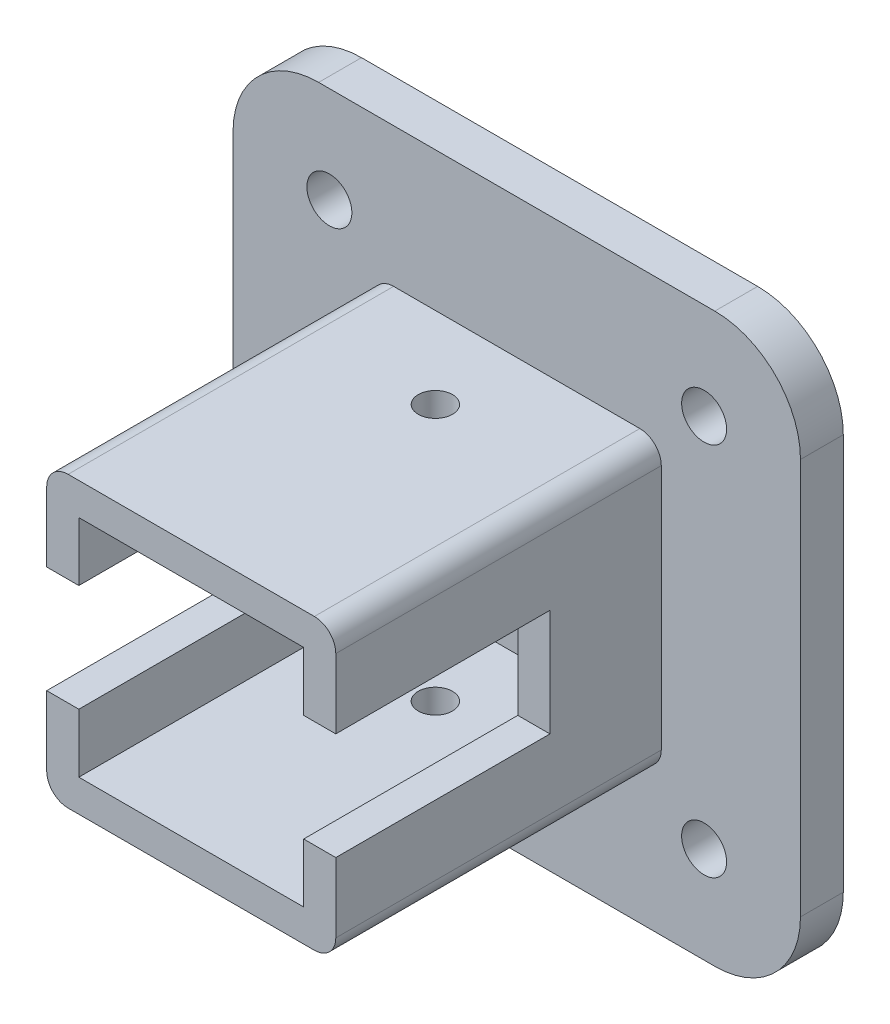
SolidWorks part; units mm, degrees
ref_plane "Front Plane" through (0, 0, 0) normal (0, 0, 1) x (1, 0, 0)
ref_plane "Top Plane" through (0, 0, 0) normal (0, 1, 0) x (1, 0, 0)
ref_plane "Right Plane" through (0, 0, 0) normal (1, 0, 0) x (0, 0, -1)
sketch "Sketch1" plane through (0, 0, 0) normal (0, 0, 1) x (1, 0, 0)
  line L0 (13.5, 13.5) -> (-13.5, 13.5)
  line L1 (10.5, -10.5) -> (-10.5, -10.5)
  line L2 (10.5, -10.5) -> (10.5, 10.5)
  line L3 (10.5, 10.5) -> (-10.5, 10.5)
  line L4 (-10.5, -10.5) -> (-10.5, 10.5)
  line L5 (10.5, -10.5) -> (-10.5, 10.5) construction
  line L6 (10.5, 10.5) -> (-10.5, -10.5) construction
  line L7 (-13.5, -13.5) -> (-13.5, 13.5)
  line L8 (13.5, -13.5) -> (-13.5, -13.5)
  line L9 (13.5, -13.5) -> (13.5, 13.5)
  point P0 (0, 0)
  dimension "D1" = 21
  dimension "D2" = 21
  dimension "D3" = 3
extrude "Boss-Extrude1" add sketch "Sketch1" along normal blind 15.2
sketch "Sketch2" plane through (0, -13.5, 0) normal (0, -1, 0) x (1, 0, 0)
  line L0 (0, 15.2) -> (0, 0) construction
  line L1 (-13.5, 15.2) -> (13.5, 15.2) construction
  line L5 (-13.5, 0) -> (13.5, 0) construction
  circle A0 centre (0, 7.6) radius 1.6
  dimension "D1" = 3.2
  dimension "D2" = 6
extrude "Cut-Extrude1" cut sketch "Sketch2" against normal through all
sketch "Sketch5" plane through (0, 0, 0) normal (0, 0, -1) x (-1, 0, 0)
  line L0 (-21.5, 18.5) -> (-21.5, -18.5)
  line L1 (-18.5, -21.5) -> (18.5, -21.5)
  line L2 (21.5, -18.5) -> (21.5, 18.5)
  line L3 (18.5, 21.5) -> (-18.5, 21.5)
  line L4 (-13.5, 13.5) -> (-13.5, -13.5)
  line L5 (13.5, 13.5) -> (-13.5, 13.5)
  line L6 (13.5, -13.5) -> (13.5, 13.5)
  line L7 (-13.5, -13.5) -> (13.5, -13.5)
  line L8 (-13.5, 13.5) -> (-13.5, -13.5)
  line L9 (13.5, 13.5) -> (-13.5, 13.5)
  line L10 (13.5, -13.5) -> (13.5, 13.5)
  line L11 (-13.5, -13.5) -> (13.5, -13.5)
  line L12 (-21.5, 21.5) -> (-13.5, 13.5) construction
  line L13 (-13.5, -13.5) -> (-21.5, -21.5) construction
  line L14 (21.5, -21.5) -> (13.5, -13.5) construction
  line L15 (21.5, 21.5) -> (13.5, 13.5) construction
  line L16 (21.5, 21.5) -> (-21.5, 21.5) construction
  line L17 (21.5, -21.5) -> (21.5, 21.5) construction
  line L18 (-21.5, -21.5) -> (21.5, -21.5) construction
  line L19 (-21.5, 21.5) -> (-21.5, -21.5) construction
  circle A0 centre (-17.5, 17.5) radius 2.1
  circle A1 centre (-17.5, -17.5) radius 2.1
  circle A2 centre (17.5, -17.5) radius 2.1
  circle A3 centre (17.5, 17.5) radius 2.1
  arc A4 (18.5, 21.5) -> (21.5, 18.5) centre (18.5, 18.5) cw
  arc A5 (21.5, -18.5) -> (18.5, -21.5) centre (18.5, -18.5) cw
  arc A6 (-18.5, -21.5) -> (-21.5, -18.5) centre (-18.5, -18.5) cw
  arc A7 (-18.5, 21.5) -> (-21.5, 18.5) centre (-18.5, 18.5) ccw
  line M14 (-13.5, 13.5) -> (-13.5, -13.5)
  line M15 (-13.5, -13.5) -> (13.5, -13.5)
  line M16 (13.5, -13.5) -> (13.5, 13.5)
  line M17 (13.5, 13.5) -> (-13.5, 13.5)
  line M18 (10.5, 10.5) -> (10.5, -10.5)
  line M19 (10.5, -10.5) -> (-10.5, -10.5)
  line M20 (-10.5, -10.5) -> (-10.5, 10.5)
  line M21 (-10.5, 10.5) -> (10.5, 10.5)
  dimension "D3" = 4.2
  dimension "D4" = 4.2
  dimension "D5" = 4.2
  dimension "D6" = 4.2
  dimension "D7" = 3
  dimension "D1" = 0
  dimension "D2" = 8
extrude "Boss-Extrude3" add sketch "Sketch5" along normal blind 4 contours M17 M14 M15 M16 M21 M18 M19 M20 | M18 M21 M20 M19 | L3 A7 L0 A6 L1 A5 L2 A4 A0 A1 A2 A3 M14 M17 M16 M15
fillet "Fillet2" radius 2 4 edges at (-13.5, -13.5, 7.6) (-13.5, 13.5, 7.6) (13.5, 13.5, 7.6) (13.5, -13.5, 7.6)
sketch "Sketch7" plane through (0, 0, 0) normal (0, 0, 1) x (1, 0, 0)
  line L0 (18.5, 26.5) -> (-18.5, 26.5)
  line L1 (-26.5, 18.5) -> (-26.5, -18.5)
  line L2 (-18.5, -26.5) -> (18.5, -26.5)
  line L3 (26.5, -18.5) -> (26.5, 18.5)
  line L4 (18.5, 21.5) -> (-18.5, 21.5)
  line L5 (-21.5, 18.5) -> (-21.5, -18.5)
  line L6 (-18.5, -21.5) -> (18.5, -21.5)
  line L7 (21.5, -18.5) -> (21.5, 18.5)
  line L8 (18.5, 21.5) -> (-18.5, 21.5)
  line L9 (-21.5, 18.5) -> (-21.5, -18.5)
  line L10 (-18.5, -21.5) -> (18.5, -21.5)
  line L11 (21.5, -18.5) -> (21.5, 18.5)
  arc A0 (-18.5, 26.5) -> (-26.5, 18.5) centre (-18.5, 18.5) ccw
  arc A1 (-26.5, -18.5) -> (-18.5, -26.5) centre (-18.5, -18.5) ccw
  arc A2 (18.5, -26.5) -> (26.5, -18.5) centre (18.5, -18.5) ccw
  arc A3 (26.5, 18.5) -> (18.5, 26.5) centre (18.5, 18.5) ccw
  arc A4 (-18.5, 21.5) -> (-21.5, 18.5) centre (-18.5, 18.5) ccw
  arc A5 (-21.5, -18.5) -> (-18.5, -21.5) centre (-18.5, -18.5) ccw
  arc A6 (18.5, -21.5) -> (21.5, -18.5) centre (18.5, -18.5) ccw
  arc A7 (21.5, 18.5) -> (18.5, 21.5) centre (18.5, 18.5) ccw
  arc A8 (-18.5, 21.5) -> (-21.5, 18.5) centre (-18.5, 18.5) ccw
  arc A9 (-21.5, -18.5) -> (-18.5, -21.5) centre (-18.5, -18.5) ccw
  arc A10 (18.5, -21.5) -> (21.5, -18.5) centre (18.5, -18.5) ccw
  arc A11 (21.5, 18.5) -> (18.5, 21.5) centre (18.5, 18.5) ccw
  dimension "D1" = 0
  dimension "D2" = 5
extrude "Boss-Extrude5" add sketch "Sketch7" against normal up to surface (4 mm away) up to face at (15.4, 17.5, -4)
sketch "Sketch8" plane through (0, 0, 15.2) normal (0, 0, 1) x (1, 0, 0)
  line L4 (-13.5, 11.5) -> (-13.5, -11.5)
  line L5 (-11.5, -13.5) -> (11.5, -13.5)
  line L6 (13.5, -11.5) -> (13.5, 11.5)
  line L7 (11.5, 13.5) -> (-11.5, 13.5)
  line L8 (-13.5, 11.5) -> (-13.5, -11.5)
  line L9 (-11.5, -13.5) -> (11.5, -13.5)
  line L10 (13.5, -11.5) -> (13.5, 11.5)
  line L11 (11.5, 13.5) -> (-11.5, 13.5)
  line L12 (-10.5, -10.5) -> (10.5, -10.5)
  line L13 (-10.5, 10.5) -> (-10.5, -10.5)
  line L14 (10.5, 10.5) -> (-10.5, 10.5)
  line L15 (10.5, -10.5) -> (10.5, 10.5)
  line L16 (-10.5, -10.5) -> (10.5, -10.5)
  line L17 (-10.5, 10.5) -> (-10.5, -10.5)
  line L18 (10.5, 10.5) -> (-10.5, 10.5)
  line L19 (10.5, -10.5) -> (10.5, 10.5)
  arc A4 (-13.5, -11.5) -> (-11.5, -13.5) centre (-11.5, -11.5) ccw
  arc A5 (11.5, -13.5) -> (13.5, -11.5) centre (11.5, -11.5) ccw
  arc A6 (13.5, 11.5) -> (11.5, 13.5) centre (11.5, 11.5) ccw
  arc A7 (-11.5, 13.5) -> (-13.5, 11.5) centre (-11.5, 11.5) ccw
  arc A8 (-13.5, -11.5) -> (-11.5, -13.5) centre (-11.5, -11.5) ccw
  arc A9 (11.5, -13.5) -> (13.5, -11.5) centre (11.5, -11.5) ccw
  arc A10 (13.5, 11.5) -> (11.5, 13.5) centre (11.5, 11.5) ccw
  arc A11 (-11.5, 13.5) -> (-13.5, 11.5) centre (-11.5, 11.5) ccw
  line M13 (-13.5, 11.5) -> (-13.5, -11.5)
  arc M14 (-13.5, -11.5) -> (-11.5, -13.5) centre (-11.5, -11.5) ccw
  line M15 (-11.5, -13.5) -> (11.5, -13.5)
  arc M16 (11.5, -13.5) -> (13.5, -11.5) centre (11.5, -11.5) ccw
  line M17 (13.5, -11.5) -> (13.5, 11.5)
  arc M18 (13.5, 11.5) -> (11.5, 13.5) centre (11.5, 11.5) ccw
  line M19 (11.5, 13.5) -> (-11.5, 13.5)
  arc M20 (-11.5, 13.5) -> (-13.5, 11.5) centre (-11.5, 11.5) ccw
  line M21 (10.5, -10.5) -> (-10.5, -10.5)
  line M22 (-10.5, -10.5) -> (-10.5, 10.5)
  line M23 (-10.5, 10.5) -> (10.5, 10.5)
  line M24 (10.5, 10.5) -> (10.5, -10.5)
  dimension "D1" = 0
  dimension "D2" = 0
extrude "Boss-Extrude7" add sketch "Sketch8" along normal blind 15.2 contours M20 M13 M14 M15 M16 M17 M18 M19 M24 M21 M22 M23
sketch "Sketch9" plane through (13.5, 0, 0) normal (1, 0, 0) x (0, 0, -1)
  line L0 (-30.4, 0) -> (0, 0) construction
  line L1 (-30.4, -11.5) -> (-30.4, 11.5) construction
  line L3 (-30.4, 5) -> (-10.4, 5)
  line L4 (-30.4, 5) -> (-30.4, -5)
  line L5 (-30.4, -5) -> (-10.4, -5)
  line L6 (-10.4, 5) -> (-10.4, -5)
  dimension "D1" = 10
  dimension "D2" = 5
  dimension "D3" = 20
extrude "Cut-Extrude2" cut sketch "Sketch9" against normal through all
